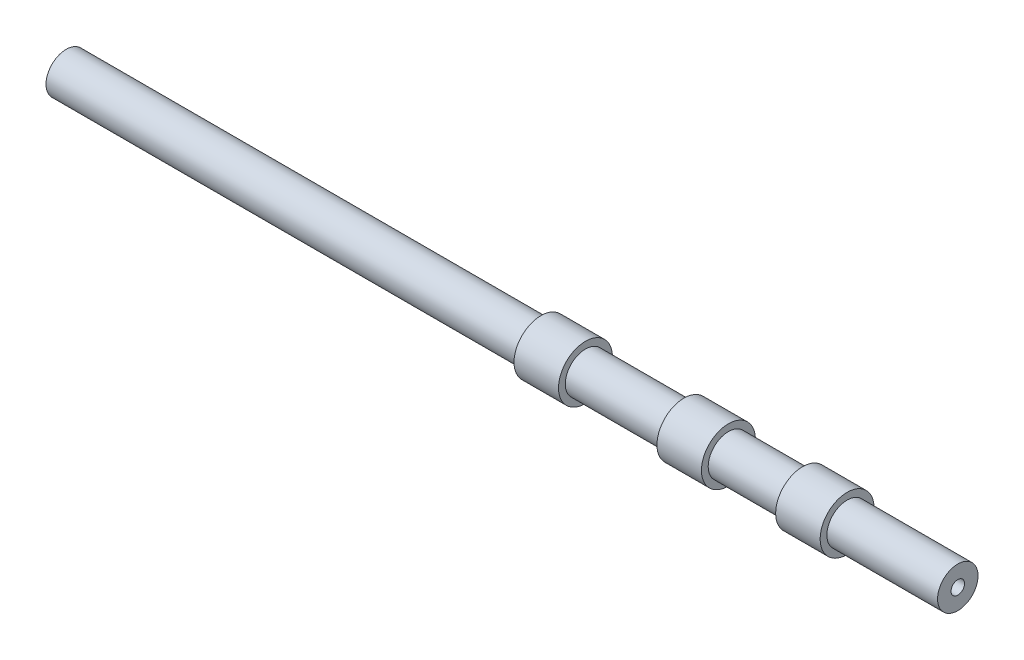
SolidWorks part; units mm, degrees
ref_plane "Front Plane" through (0, 0, 0) normal (0, 0, 1) x (1, 0, 0)
ref_plane "Top Plane" through (0, 0, 0) normal (0, 1, 0) x (1, 0, 0)
ref_plane "Right Plane" through (0, 0, 0) normal (1, 0, 0) x (0, 0, -1)
sketch "Sketch1" plane through (0, 0, 0) normal (0, 0, 1) x (1, 0, 0)
  line L0 (-141.8295, 0) -> (141.8295, 0) construction
  line L1 (286.0935, 15) -> (204.0635, 15)
  line L2 (204.0635, 15) -> (204.0635, 20)
  line L3 (204.0635, 20) -> (171.0935, 20)
  line L4 (171.0935, 20) -> (171.0935, 15)
  line L5 (171.0935, 15) -> (116.0935, 15)
  line L6 (116.0935, 15) -> (116.0935, 20)
  line L7 (116.0935, 20) -> (83.1235, 20)
  line L8 (83.1235, 20) -> (83.1235, 15)
  line L9 (83.1235, 15) -> (10.1535, 15)
  line L10 (10.1535, 15) -> (10.1535, 20)
  line L11 (10.1535, 20) -> (-22.8165, 20)
  line L12 (-22.8165, 20) -> (-22.8165, 15)
  line L13 (-22.8165, 15) -> (-143.2765, 15)
  line L14 (-143.2765, 15) -> (-374.6965, 15)
  point P4 (0, 0)
  dimension "D1" = 115
  dimension "D2" = 20
  dimension "D3" = 660.79
  dimension "D4" = 20
  dimension "D5" = 15
  dimension "D6" = 20
  dimension "D8" = 32.97
  dimension "D9" = 55
  dimension "D10" = 32.97
  dimension "D11" = 72.97
  dimension "D12" = 32.97
revolve "Revolve-Thin1" add sketch "Sketch1" angle 360 about L0 wall 10
